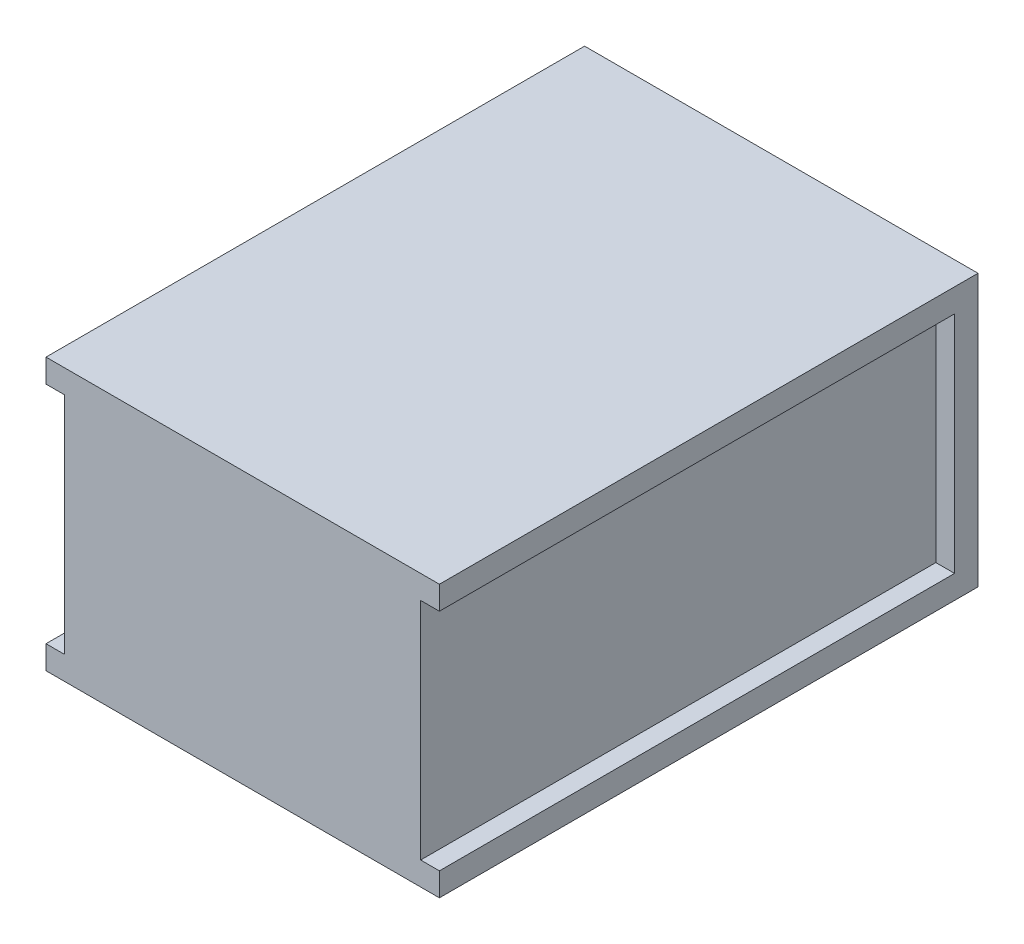
SolidWorks part; units mm, degrees
ref_plane "Plan de face" through (0, 0, 0) normal (0, 0, 1) x (1, 0, 0)
ref_plane "Plan de dessus" through (0, 0, 0) normal (0, 1, 0) x (1, 0, 0)
ref_plane "Plan de droite" through (0, 0, 0) normal (1, 0, 0) x (0, 0, -1)
sketch "Esquisse1" plane through (0, 0, 0) normal (0, 1, 0) x (1, 0, 0)
  line L0 (-42, 57.5) -> (42, -57.5) construction
  line L1 (-42, 57.5) -> (42, 57.5)
  line L2 (-42, 57.5) -> (-42, -57.5)
  line L3 (-42, -57.5) -> (42, -57.5)
  line L4 (42, 57.5) -> (42, -57.5)
  dimension "D1" = 115
  dimension "D2" = 84
extrude "Boss.-Extru.1" add sketch "Esquisse1" along normal blind 58
sketch "Esquisse2" plane through (-42, 0, 0) normal (-1, 0, 0) x (0, 0, 1)
  line L0 (57.5, 58) -> (57.5, 0) construction
  line L1 (57.5, 53) -> (-52.5, 53)
  line L2 (57.5, 53) -> (57.5, 5)
  line L3 (57.5, 5) -> (-52.5, 5)
  line L4 (-52.5, 53) -> (-52.5, 5)
  line L5 (57.5, 29) -> (-10.3389, 29) construction
  line L6 (-57.5, 0) -> (57.5, 0) construction
  line L7 (-57.5, 58) -> (57.5, 58) construction
  line L8 (-57.5, 58) -> (-57.5, 0) construction
  point P12 (0, 58)
  dimension "D1" = 5
  dimension "D2" = 5
extrude "Enlèv. mat.-Extru.1" cut sketch "Esquisse2" against normal blind 4
mirror "Symétrie1" about plane through (0, 0, 0) normal (1, 0, 0) of "Enlèv. mat.-Extru.1"
